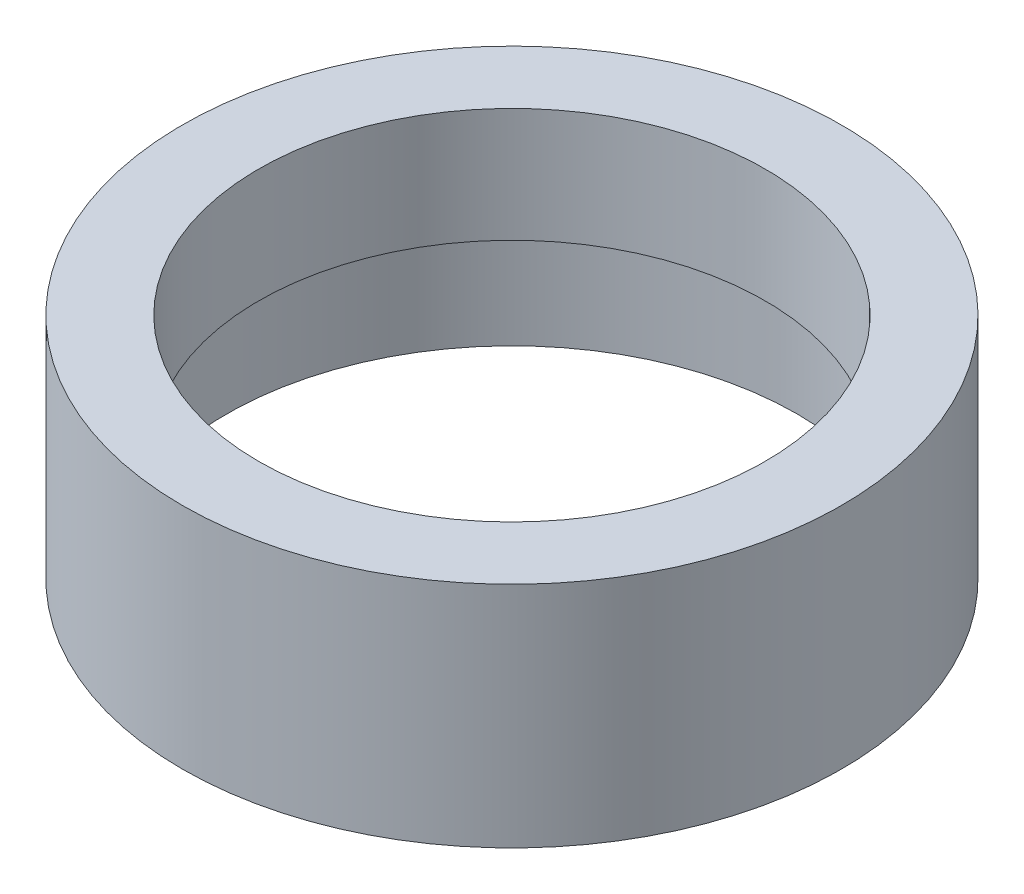
SolidWorks part; units mm, degrees
ref_plane "前视基准面" through (0, 0, 0) normal (0, 0, 1) x (1, 0, 0)
ref_plane "上视基准面" through (0, 0, 0) normal (0, 1, 0) x (1, 0, 0)
ref_plane "右视基准面" through (0, 0, 0) normal (1, 0, 0) x (0, 0, -1)
sketch "草图1" plane through (0, 0, 0) normal (0, 0, 1) x (1, 0, 0)
  line L0 (0, 60.0208) -> (0, -56.4315) construction
  line L1 (13.75, 0) -> (13.75, 4.5)
  line L2 (13.75, 4.5) -> (14.35, 4.5)
  line L3 (14.35, 4.5) -> (14.35, 5.5)
  line L4 (14.35, 5.5) -> (12.2, 5.5)
  line L5 (12.2, 5.5) -> (12.2, 11)
  line L6 (12.2, 11) -> (15.875, 11)
  line L7 (15.875, 11) -> (15.875, 0)
  line L8 (15.875, 0) -> (13.75, 0)
  point P5 (13.275, 5.5)
  dimension "D1" = 15.875
  dimension "D2" = 12.2
  dimension "D3" = 14.35
  dimension "D4" = 13.75
  dimension "D5" = 1
  dimension "D6" = 5.5
  dimension "D7" = 11
revolve "旋转1" add sketch "草图1" angle 360 about L0
cosmetic thread "装饰螺纹线1" parameters "D2"=25.4
cosmetic thread "装饰螺纹线2" parameters "D2"=28.5
